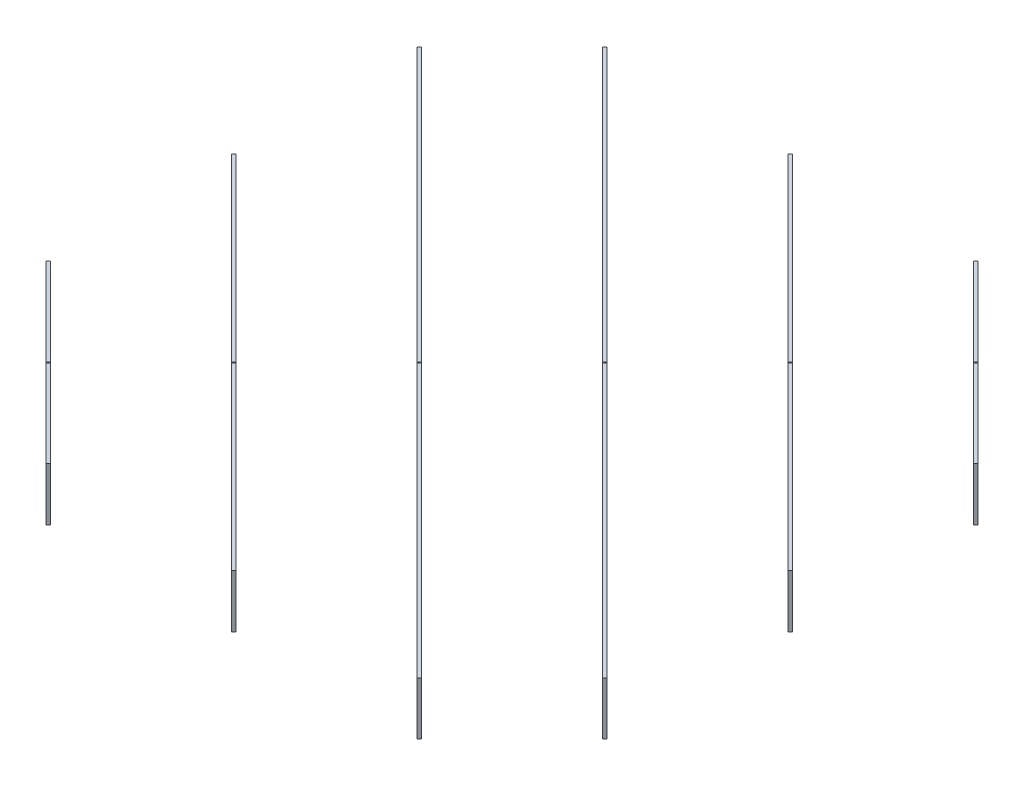
SolidWorks part; units mm, degrees
material "Plain Carbon Steel"
ref_plane "Front" through (0, 0, 0) normal (0, 0, 1) x (1, 0, 0)
ref_plane "Top" through (0, 0, 0) normal (0, 1, 0) x (1, 0, 0)
ref_plane "Right" through (0, 0, 0) normal (1, 0, 0) x (0, 0, -1)
sketch "Sketch1" plane through (0, 0, 0) normal (0, 1, 0) x (1, 0, 0)
  line L0 (-525, -525) -> (-525, 525) construction
  line L1 (-605, 605) -> (605, 605) construction
  line L2 (-605, 605) -> (-605, -605) construction
  line L3 (-605, -605) -> (605, -605) construction
  line L4 (605, 605) -> (605, -605) construction
  line L5 (-605, 605) -> (605, -605) construction
  line L6 (-605, -605) -> (605, 605) construction
  line L7 (-525, 525) -> (525, 525) construction
  line L8 (-525, 350) -> (525, 350) construction
  line L9 (-525, 175) -> (525, 175) construction
  line L10 (-525, 0) -> (525, 0) construction
  line L11 (-525, -175) -> (525, -175) construction
  line L12 (-525, -350) -> (525, -350) construction
  line L13 (-525, -525) -> (525, -525) construction
  line L14 (-350, -525) -> (-350, 525) construction
  line L15 (-175, -525) -> (-175, 525) construction
  line L16 (0, -525) -> (0, 525) construction
  line L17 (175, -525) -> (175, 525) construction
  line L18 (350, -525) -> (350, 525) construction
  line L19 (525, -525) -> (525, 525) construction
  point P0 (0, 0)
  dimension "D1" = 1210
  dimension "D2" = 1210
  dimension "D5" = 175
  dimension "D3" = 7
  dimension "D4" = 7
sketch "Sketch2" plane through (0, 0, 0) normal (0, 1, 0) x (1, 0, 0)
  line L0 (-605, -274.2426) -> (-274.2426, -605)
  line L1 (-602.8787, 602.8787) -> (602.8787, 602.8787) construction
  line L2 (-602.8787, 602.8787) -> (-602.8787, -602.8787) construction
  line L3 (-602.8787, -602.8787) -> (602.8787, -602.8787) construction
  line L4 (602.8787, 602.8787) -> (602.8787, -602.8787) construction
  line L5 (-602.8787, 602.8787) -> (602.8787, -602.8787) construction
  line L6 (-602.8787, -602.8787) -> (602.8787, 602.8787) construction
  line L7 (-605, 605) -> (605, -605) construction
  line L8 (-427.8787, 602.8787) -> (602.8787, -427.8787) construction
  line L9 (-77.8787, 602.8787) -> (602.8787, -77.8787) construction
  line L10 (272.1213, 602.8787) -> (602.8787, 272.1213) construction
  line L11 (-602.8787, -272.1213) -> (-272.1213, -602.8787) construction
  line L12 (-602.8787, 77.8787) -> (77.8787, -602.8787) construction
  line L13 (-602.8787, 427.8787) -> (427.8787, -602.8787) construction
  line L14 (-605, 75.7574) -> (75.7574, -605)
  line L15 (-605, 425.7574) -> (425.7574, -605)
  line L16 (-430, 600.7574) -> (600.7574, -430)
  line L17 (-80, 600.7574) -> (600.7574, -80)
  line L18 (270, 600.7574) -> (600.7574, 270)
  line L19 (-600.7574, -270) -> (-270, -600.7574)
  line L20 (-600.7574, 80) -> (80, -600.7574)
  line L21 (-600.7574, 430) -> (430, -600.7574)
  line L22 (-425.7574, 605) -> (605, -425.7574)
  line L23 (-75.7574, 605) -> (605, -75.7574)
  line L24 (274.2426, 605) -> (605, 274.2426)
  line L25 (-605, -274.2426) -> (-600.7574, -270)
  line L26 (-274.2426, -605) -> (-270, -600.7574)
  line L27 (-605, 75.7574) -> (-600.7574, 80)
  line L28 (75.7574, -605) -> (80, -600.7574)
  line L29 (-605, 425.7574) -> (-600.7574, 430)
  line L30 (425.7574, -605) -> (430, -600.7574)
  line L31 (-430, 600.7574) -> (-425.7574, 605)
  line L32 (600.7574, -430) -> (605, -425.7574)
  line L33 (-80, 600.7574) -> (-75.7574, 605)
  line L34 (600.7574, -80) -> (605, -75.7574)
  line L35 (270, 600.7574) -> (274.2426, 605)
  line L36 (600.7574, 270) -> (605, 274.2426)
  line L38 (-605, 605) -> (605, 605) construction
  line L39 (605, 605) -> (605, -605) construction
extrude "Boss-Extrude1" add sketch "Sketch2" along normal blind 100
sketch "Sketch3" plane through (-439.6213, 0, 439.6213) normal (-0.7071, 0, 0.7071) x (0.7071, 0, 0.7071)
  line L0 (-742.4621, 0) -> (0, 0) construction
  line L1 (-126.7056, 50) -> (-120.7056, 50)
  line L2 (-126.7056, 50) -> (-126.7056, -50)
  line L3 (-126.7056, -50) -> (-120.7056, -50)
  line L4 (-120.7056, 50) -> (-120.7056, -50)
  line L5 (-126.7056, 50) -> (-120.7056, -50) construction
  line L6 (-126.7056, -50) -> (-120.7056, 50) construction
  line L7 (123.7437, 0) -> (-618.7184, 0) construction
  line L8 (-374.2311, 50) -> (-368.2311, 50)
  line L9 (-374.2311, 50) -> (-374.2311, -50)
  line L10 (-374.2311, -50) -> (-368.2311, -50)
  line L11 (-368.2311, 50) -> (-368.2311, -50)
  line L12 (-374.2311, 50) -> (-368.2311, -50) construction
  line L13 (-374.2311, -50) -> (-368.2311, 50) construction
  line L14 (-621.7184, 50) -> (-615.7184, 50)
  line L15 (-621.7184, 50) -> (-621.7184, -50)
  line L16 (-621.7184, -50) -> (-615.7184, -50)
  line L17 (-615.7184, 50) -> (-615.7184, -50)
  line L18 (-621.7184, 50) -> (-615.7184, -50) construction
  line L19 (-621.7184, -50) -> (-615.7184, 50) construction
  line L20 (0, 0) -> (0, 100) construction
  line L21 (-233.8808, 100) -> (233.8808, 100) construction
  line L22 (621.7184, -50) -> (615.7184, 50) construction
  line L23 (621.7184, 50) -> (615.7184, -50) construction
  line L24 (374.2311, -50) -> (368.2311, 50) construction
  line L25 (374.2311, 50) -> (368.2311, -50) construction
  line L26 (126.7056, -50) -> (120.7056, 50) construction
  line L27 (126.7056, 50) -> (120.7056, -50) construction
  line L28 (615.7184, 50) -> (615.7184, -50)
  line L29 (621.7184, -50) -> (615.7184, -50)
  line L30 (621.7184, 50) -> (621.7184, -50)
  line L31 (621.7184, 50) -> (615.7184, 50)
  line L32 (368.2311, 50) -> (368.2311, -50)
  line L33 (374.2311, -50) -> (368.2311, -50)
  line L34 (374.2311, 50) -> (374.2311, -50)
  line L35 (374.2311, 50) -> (368.2311, 50)
  line L36 (120.7056, 50) -> (120.7056, -50)
  line L37 (126.7056, -50) -> (120.7056, -50)
  line L38 (126.7056, 50) -> (126.7056, -50)
  line L39 (126.7056, 50) -> (120.7056, 50)
  circle A0 centre (-126.7056, 50) radius 1.5
  circle A1 centre (-120.7056, 50) radius 1.5
  circle A2 centre (-621.7184, 50) radius 1.5
  circle A3 centre (-615.7184, 50) radius 1.5
  circle A4 centre (-374.2311, 50) radius 1.5
  circle A5 centre (-368.2311, 50) radius 1.5
  circle A6 centre (368.2311, 50) radius 1.5
  circle A7 centre (374.2311, 50) radius 1.5
  circle A8 centre (615.7184, 50) radius 1.5
  circle A9 centre (621.7184, 50) radius 1.5
  circle A10 centre (120.7056, 50) radius 1.5
  circle A11 centre (126.7056, 50) radius 1.5
  point P0 (-123.7056, 0)
  point P7 (-371.2311, 0)
  point P12 (-618.7184, 0)
  point P48 (618.7184, 0)
  point P49 (371.2311, 0)
  point P50 (123.7056, 0)
  line M15 (-233.8808, 0) -> (233.8808, 0)
  dimension "D1" = 100
  dimension "D7" = 3
  dimension "D8" = 3
  dimension "D9" = 3
  dimension "D10" = 3
  dimension "D11" = 3
  dimension "D12" = 3
  dimension "D2" = 100
  dimension "D3" = 100
  dimension "D4" = 3
  dimension "D5" = 3
  dimension "D6" = 3
extrude "Cut-Extrude1" cut sketch "Sketch3" against normal through all contours A3 L14 A2 L15 L16 L17 | L14 A2 L15 | L17 A3 L14 | L14 A3 L17 | L15 A2 L14 | L8 A4 L9 | L9 A4 L8 | A5 L8 A4 L9 L10 L11 | L8 A5 L11 | L11 A5 L8 | L1 A0 L2 | L4 A1 L1 | L1 A1 L4 | A1 L1 A0 L2 L4 M15 | L2 A0 L1 | A10 L36 L39 | A10 L39 L36 | L38 A11 L39 A10 L36 M15 | A11 L38 L39 | A11 L39 L38 | A6 L32 L35 | L34 A7 L35 A6 L32 L33 | A7 L35 L34 | A7 L34 L35 | A6 L35 L32 | A8 L28 L31 | A9 L31 L30 | L30 A9 L31 A8 L28 L29 | A9 L30 L31 | A8 L31 L28
sketch "Sketch4" plane through (260.3787, 0, -260.3787) normal (-0.7071, 0, 0.7071) x (0.7071, 0, 0.7071)
  line L0 (0.0191, 25) -> (0.0191, 19) construction
  line L5 (15.0191, 25) -> (-14.9809, 25) construction
  line L6 (-14.9809, 19) -> (15.0191, 19) construction
  line L11 (25.0191, 25) -> (25.0191, 19) construction
  line L12 (-27.9809, 28) -> (28.0191, 28)
  line L13 (-27.9809, 28) -> (-27.9809, 16)
  line L14 (-27.9809, 16) -> (28.0191, 16)
  line L15 (28.0191, 28) -> (28.0191, 16)
  line L16 (-27.9809, 28) -> (28.0191, 16) construction
  line L17 (-27.9809, 16) -> (28.0191, 28) construction
  point P5 (0.0191, 22)
  dimension "D1" = 3
  dimension "D2" = 3
extrude "Cut-Extrude2" cut sketch "Sketch4" against normal up to next (6 mm away)
sketch "Sketch5" plane through (-264.6213, 0, 264.6213) normal (-0.7071, 0, 0.7071) x (0.7071, 0, 0.7071)
  line L4 (-27.9809, 28) -> (-27.9809, 16)
  line L5 (-27.9809, 28) -> (-27.9809, 16)
  line L6 (28.0191, 28) -> (-27.9809, 28)
  line L7 (28.0191, 28) -> (-27.9809, 28)
  line L12 (28.0191, 16) -> (28.0191, 28)
  line L13 (28.0191, 16) -> (28.0191, 28)
  line L14 (-27.9809, 16) -> (28.0191, 16)
  line L15 (-27.9809, 16) -> (28.0191, 16)
  dimension "D1" = 0
extrude "Cut-Extrude3" cut sketch "Sketch5" against normal up to next (6 mm away)
sketch "Sketch6" plane through (-439.6213, 0, 439.6213) normal (-0.7071, 0, 0.7071) x (0.7071, 0, 0.7071)
  line L0 (0, 0) -> (0, 100) construction
  line L1 (-120.7056, 0) -> (120.7056, 0) construction
  line L2 (-233.8808, 100) -> (233.8808, 100) construction
  circle A1 centre (0, 100) radius 1.5
  dimension "D1" = 3
extrude "Cut-Extrude4" cut sketch "Sketch6" against normal through all
sketch "Sketch7" plane through (-89.6213, 0, 89.6213) normal (-0.7071, 0, 0.7071) x (0.7071, 0, 0.7071)
  circle A0 centre (0, 84) radius 4
  circle A1 centre (0, 64) radius 4
  dimension "D1" = 8
extrude "Cut-Extrude5" cut sketch "Sketch7" against normal up to surface (253.4874 mm away)
sketch "Sketch8" plane through (-439.6213, 0, 439.6213) normal (-0.7071, 0, 0.7071) x (0.7071, 0, 0.7071)
  line L0 (-1.5, 100) -> (1.5, 100) construction
  line L1 (0, 100) -> (0, 0) construction
  line L2 (-120.7056, 0) -> (120.7056, 0) construction
  circle A0 centre (0, 50) radius 3
  dimension "D1" = 6
extrude "Cut-Extrude6" cut sketch "Sketch8" against normal up to surface (253.4874 mm away)
sketch "Sketch9" plane through (439.6213, 0, -439.6213) normal (0.7071, 0, -0.7071) x (-0.7071, 0, -0.7071)
  circle A1 centre (0, 50) radius 3
  circle A2 centre (0, 50) radius 3
  dimension "D1" = 0
extrude "Cut-Extrude7" cut sketch "Sketch9" against normal up to surface (253.4874 mm away)
sketch "Sketch10" plane through (-264.6213, 0, 264.6213) normal (-0.7071, 0, 0.7071) x (0.7071, 0, 0.7071)
  line L0 (-368.2311, 100) -> (-126.7437, 100) construction
  line L1 (-481.3681, 100) -> (-1.5, 100) construction
  line L4 (-126.7437, 51.5) -> (-126.7437, 100) construction
  line L5 (-368.2311, 100) -> (-368.2311, 51.5) construction
  line L6 (-247.4874, 100) -> (-247.4683, 0) construction
  line L7 (-368.2311, 0) -> (-126.7056, 0) construction
  circle A0 centre (-247.4778, 50) radius 3
  dimension "D1" = 6
extrude "Cut-Extrude8" cut sketch "Sketch10" against normal up to surface (748.4621 mm away) up to face at (266.7426, 50, -262.5)
sketch "Sketch11" plane through (-89.6213, 0, 89.6213) normal (-0.7071, 0, 0.7071) x (0.7071, 0, 0.7071)
  line L0 (-615.7184, 0) -> (-374.2311, 0) construction
  line L1 (-494.9747, 0) -> (-494.9747, 100) construction
  line L2 (-728.8555, 100) -> (-1.5, 100) construction
  circle A0 centre (-494.9747, 50) radius 3
  dimension "D1" = 6
extrude "Cut-Extrude9" cut sketch "Sketch11" against normal up to surface (253.4874 mm away)
ref_plane "Plane1" through (0, 0, 0) normal (-0.7071, 0, -0.7071) x (-0.7071, 0, 0.7071)
mirror "Mirror1" about plane through (0, 0, 0) normal (-0.7071, 0, -0.7071) of "Cut-Extrude9", "Cut-Extrude8"
equation "\"Plate width\"= 100mm"
equation "\"D1@Boss-Extrude1\"=\"Plate width\""
equation "\"D1@Sketch3\"=\"Plate width\""
equation "\"D2@Sketch3\"=\"Plate width\""
equation "\"D3@Sketch3\"=\"Plate width\""
equation "\"D4@Sketch3\"=\"half plate thickness\""
equation "\"D5@Sketch3\"=\"half plate thickness\""
equation "\"D6@Sketch3\"=\"half plate thickness\""
equation "\"D7@Sketch3\"=\"half plate thickness\""
equation "\"D8@Sketch3\"=\"half plate thickness\""
equation "\"D9@Sketch3\"=\"half plate thickness\""
equation "\"D10@Sketch3\"=\"half plate thickness\""
equation "\"D11@Sketch3\"=\"half plate thickness\""
equation "\"D12@Sketch3\"=\"half plate thickness\""
